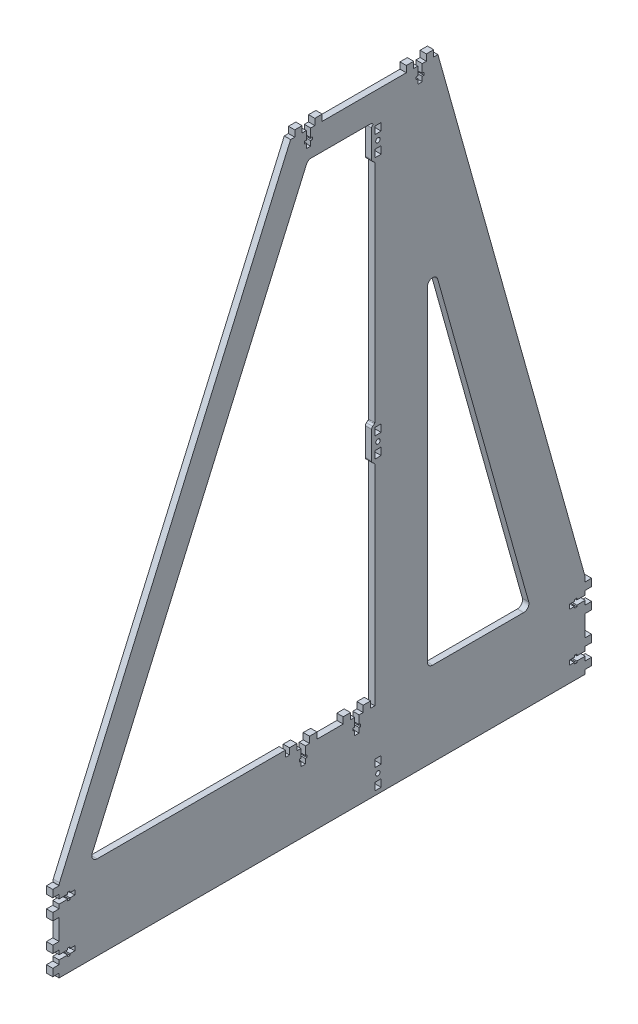
SolidWorks part; units mm, degrees
material "Клен"
ref_plane "Спереди" through (0, 0, 0) normal (0, 0, 1) x (1, 0, 0)
ref_plane "Сверху" through (0, 0, 0) normal (0, 1, 0) x (1, 0, 0)
ref_plane "Справа" through (0, 0, 0) normal (1, 0, 0) x (0, 0, -1)
sketch "боковина" plane through (0, 0, 0) normal (1, 0, 0) x (0, 0, -1)
  line L0 (-623.8891, -244.3792) -> (-123.8891, -244.3792)
  line L1 (-123.8891, -244.3792) -> (-123.8891, -165.066)
  line L2 (-124.0743, -163.7178) -> (-263.8891, 335.6208)
  line L3 (-263.8891, 335.6208) -> (-313.8032, 335.6208)
  line L4 (-323.8891, 305.6208) -> (-323.8891, -164.3792)
  line L5 (-408.8787, -164.3792) -> (-587.7577, -164.3792)
  line L6 (-623.8891, -168.1598) -> (-623.8891, -244.3792)
  line L7 (-268.8891, -164.3792) -> (-182.4044, -164.3792)
  line L8 (-177.5896, -158.031) -> (-264.0743, 150.8428)
  line L9 (-273.8891, 149.4947) -> (-273.8891, -159.3792)
  line L10 (-623.4697, -166.1553) -> (-403.8891, 335.6208)
  line L11 (-403.8891, 335.6208) -> (-313.8032, 335.6208)
  line L12 (-592.3383, -157.3747) -> (-388.8512, 307.6253)
  line L13 (-384.2706, 310.6208) -> (-328.8891, 310.6208)
  line L14 (-323.8891, -164.3792) -> (-323.8891, -170.3792)
  line L15 (-323.8891, -170.3792) -> (-408.8787, -170.3792)
  line L16 (-408.8787, -170.3792) -> (-408.8787, -164.3792)
  arc A0 (-264.0743, 150.8428) -> (-273.8891, 149.4947) centre (-268.8891, 149.4947) ccw
  arc A1 (-182.4044, -164.3792) -> (-177.5896, -158.031) centre (-182.4044, -159.3792) ccw
  arc A2 (-268.8891, -164.3792) -> (-273.8891, -159.3792) centre (-268.8891, -159.3792) cw
  arc A4 (-592.3383, -157.3747) -> (-587.7577, -164.3792) centre (-587.7577, -159.3792) ccw
  arc A5 (-328.8891, 310.6208) -> (-323.8891, 305.6208) centre (-328.8891, 305.6208) cw
  arc A6 (-384.2706, 310.6208) -> (-388.8512, 307.6253) centre (-384.2706, 305.6208) ccw
  arc A7 (-623.4697, -166.1553) -> (-623.8891, -168.1598) centre (-618.8891, -168.1598) ccw
  arc A8 (-123.8891, -165.066) -> (-124.0743, -163.7178) centre (-128.8891, -165.066) ccw
  point P25 (-323.8891, -164.3792)
  point P34 (-623.8891, -167.1137)
  point P37 (-123.8891, -164.3792)
  point P38 (-358.8462, 335.6208)
  dimension "D10" = 5
  dimension "D11" = 5
  dimension "D12" = 5
  dimension "D1" = 80
  dimension "D2" = 60
  dimension "D6" = 300
  dimension "D7" = 50
  dimension "D8" = 50
  dimension "D4" = 500
  dimension "D5" = 80
  dimension "D3" = 200
  dimension "D9" = 25
  dimension "D13" = 80
  dimension "D14" = 25
  dimension "D15" = 6
extrude "Бобышка-боковина" add sketch "боковина" along normal blind 6
ref_plane "Плоскость1" through (3, 0, 0) normal (1, 0, 0) x (0, 0, -1)
sketch "Эскиз2" plane through (6, 285.6208, 386.8891) normal (1, 0, 0) x (0, 0, -1)
  line L1 (-13.0318, 50) -> (-6.0318, 50)
  line L2 (-13.0318, 50) -> (-13.0318, 56)
  line L3 (-13.0318, 56) -> (-6.0318, 56)
  line L4 (-6.0318, 50) -> (-6.0318, 56)
  line L5 (13, 56) -> (-13, 56) construction
  line L7 (13.0318, 50) -> (6.0318, 50)
  line L8 (6.0318, 50) -> (6.0318, 56)
  line L9 (13.0318, 56) -> (6.0318, 56)
  line L10 (13.0318, 50) -> (13.0318, 56)
  dimension "D1" = 7
extrude "Бобышка-Вытянуть2" add sketch "Эскиз2" against normal blind 6
sketch "Эскиз3" plane through (6, 285.6208, 386.8891) normal (1, 0, 0) x (0, 0, -1)
  line L3 (-2.1, 42) -> (-3.6, 42)
  line L4 (-3.6, 42) -> (-3.6, 39.6)
  line L5 (-3.6, 39.6) -> (-2.1, 39.6)
  line L11 (3.6, 39.6) -> (2.1, 39.6)
  line L12 (3.6, 42) -> (3.6, 39.6)
  line L13 (2.1, 42) -> (3.6, 42)
  line L16 (-2.1, 42) -> (-2.1, 50)
  line L17 (-2.1, 50) -> (2.1, 50)
  line L18 (2.1, 50) -> (2.1, 42)
  line L19 (2.1, 39.6) -> (2.1, 35)
  line L20 (2.1, 35) -> (-2.1, 35)
  line L21 (-2.1, 35) -> (-2.1, 39.6)
  line L22 (13, 50) -> (-13, 50) construction
  point P15 (0, 43.65)
  point P20 (0, 50)
  dimension "D2" = 7.2
  dimension "D3" = 2.4
  dimension "D4" = 4.2
  dimension "D5" = 15
extrude "Вырез-Вытянуть1" cut sketch "Эскиз3" against normal through all
other "Авто-элемент1<DIN967-1>"
sketch "Эскиз21" plane through (6, 285.6208, 280.8891) normal (1, 0, 0) x (0, 0, -1)
  line L1 (-13.0318, 50) -> (-6.0318, 50)
  line L2 (-13.0318, 50) -> (-13.0318, 56)
  line L3 (-13.0318, 56) -> (-6.0318, 56)
  line L4 (-6.0318, 50) -> (-6.0318, 56)
  line L5 (13, 56) -> (-13, 56) construction
  line L7 (13.0318, 50) -> (6.0318, 50)
  line L8 (6.0318, 50) -> (6.0318, 56)
  line L9 (13.0318, 56) -> (6.0318, 56)
  line L10 (13.0318, 50) -> (13.0318, 56)
  dimension "D1" = 7
extrude "Бобышка-Вытянуть21" add sketch "Эскиз21" against normal blind 6
sketch "Эскиз31" plane through (6, 285.6208, 280.8891) normal (1, 0, 0) x (0, 0, -1)
  line L3 (-2.1, 42) -> (-3.6, 42)
  line L4 (-3.6, 42) -> (-3.6, 39.6)
  line L5 (-3.6, 39.6) -> (-2.1, 39.6)
  line L11 (3.6, 39.6) -> (2.1, 39.6)
  line L12 (3.6, 42) -> (3.6, 39.6)
  line L13 (2.1, 42) -> (3.6, 42)
  line L16 (-2.1, 42) -> (-2.1, 50)
  line L17 (-2.1, 50) -> (2.1, 50)
  line L18 (2.1, 50) -> (2.1, 42)
  line L19 (2.1, 39.6) -> (2.1, 35)
  line L20 (2.1, 35) -> (-2.1, 35)
  line L21 (-2.1, 35) -> (-2.1, 39.6)
  line L22 (13, 50) -> (-13, 50) construction
  point P15 (0, 43.65)
  point P20 (0, 50)
  dimension "D2" = 7.2
  dimension "D3" = 2.4
  dimension "D4" = 4.2
  dimension "D5" = 15
extrude "Вырез-Вытянуть11" cut sketch "Эскиз31" against normal through all
other "Авто-элемент2<DIN967-2>"
sketch "Эскиз22" plane through (0, 285.6208, 386.8891) normal (-1, 0, 0) x (0, 0, 1)
  line L1 (-13.0318, 50) -> (-6.0318, 50)
  line L2 (-13.0318, 50) -> (-13.0318, 56)
  line L3 (-13.0318, 56) -> (-6.0318, 56)
  line L4 (-6.0318, 50) -> (-6.0318, 56)
  line L5 (13, 56) -> (-13, 56) construction
  line L7 (13.0318, 50) -> (6.0318, 50)
  line L8 (6.0318, 50) -> (6.0318, 56)
  line L9 (13.0318, 56) -> (6.0318, 56)
  line L10 (13.0318, 50) -> (13.0318, 56)
  dimension "D1" = 7
extrude "Бобышка-Вытянуть22" add sketch "Эскиз22" against normal blind 6
other "Авто-элемент3<DIN967-3>"
sketch "Эскиз23" plane through (0, 285.6208, 280.8891) normal (-1, 0, 0) x (0, 0, 1)
  line L1 (-13.0318, 50) -> (-6.0318, 50)
  line L2 (-13.0318, 50) -> (-13.0318, 56)
  line L3 (-13.0318, 56) -> (-6.0318, 56)
  line L4 (-6.0318, 50) -> (-6.0318, 56)
  line L5 (13, 56) -> (-13, 56) construction
  line L7 (13.0318, 50) -> (6.0318, 50)
  line L8 (6.0318, 50) -> (6.0318, 56)
  line L9 (13.0318, 56) -> (6.0318, 56)
  line L10 (13.0318, 50) -> (13.0318, 56)
  dimension "D1" = 7
extrude "Бобышка-Вытянуть23" add sketch "Эскиз23" against normal blind 6
other "Авто-элемент4<DIN967-4>"
sketch "Эскиз24" plane through (0, -181.4615, 573.8891) normal (-1, 0, 0) x (0, -1, 0)
  line L1 (-13.0318, 50) -> (-6.0318, 50)
  line L2 (-13.0318, 50) -> (-13.0318, 56)
  line L3 (-13.0318, 56) -> (-6.0318, 56)
  line L4 (-6.0318, 50) -> (-6.0318, 56)
  line L5 (13, 56) -> (-13, 56) construction
  line L7 (13.0318, 50) -> (6.0318, 50)
  line L8 (6.0318, 50) -> (6.0318, 56)
  line L9 (13.0318, 56) -> (6.0318, 56)
  line L10 (13.0318, 50) -> (13.0318, 56)
  dimension "D1" = 7
extrude "Бобышка-Вытянуть24" add sketch "Эскиз24" against normal blind 6
sketch "Эскиз34" plane through (0, -181.4615, 573.8891) normal (-1, 0, 0) x (0, -1, 0)
  line L3 (-2.1, 42) -> (-3.6, 42)
  line L4 (-3.6, 42) -> (-3.6, 39.6)
  line L5 (-3.6, 39.6) -> (-2.1, 39.6)
  line L11 (3.6, 39.6) -> (2.1, 39.6)
  line L12 (3.6, 42) -> (3.6, 39.6)
  line L13 (2.1, 42) -> (3.6, 42)
  line L16 (-2.1, 42) -> (-2.1, 50)
  line L17 (-2.1, 50) -> (2.1, 50)
  line L18 (2.1, 50) -> (2.1, 42)
  line L19 (2.1, 39.6) -> (2.1, 35)
  line L20 (2.1, 35) -> (-2.1, 35)
  line L21 (-2.1, 35) -> (-2.1, 39.6)
  line L22 (13, 50) -> (-13, 50) construction
  point P15 (0, 43.65)
  point P20 (0, 50)
  dimension "D2" = 7.2
  dimension "D3" = 2.4
  dimension "D4" = 4.2
  dimension "D5" = 15
extrude "Вырез-Вытянуть14" cut sketch "Эскиз34" against normal through all
other "Авто-элемент5<DIN967-5>"
sketch "Эскиз25" plane through (0, -227.3792, 573.8891) normal (-1, 0, 0) x (0, -1, 0)
  line L1 (-13.0318, 50) -> (-6.0318, 50)
  line L2 (-13.0318, 50) -> (-13.0318, 56)
  line L3 (-13.0318, 56) -> (-6.0318, 56)
  line L4 (-6.0318, 50) -> (-6.0318, 56)
  line L5 (13, 56) -> (-13, 56) construction
  line L7 (13.0318, 50) -> (6.0318, 50)
  line L8 (6.0318, 50) -> (6.0318, 56)
  line L9 (13.0318, 56) -> (6.0318, 56)
  line L10 (13.0318, 50) -> (13.0318, 56)
  dimension "D1" = 7
extrude "Бобышка-Вытянуть25" add sketch "Эскиз25" against normal blind 6
sketch "Эскиз35" plane through (0, -227.3792, 573.8891) normal (-1, 0, 0) x (0, -1, 0)
  line L3 (-2.1, 42) -> (-3.6, 42)
  line L4 (-3.6, 42) -> (-3.6, 39.6)
  line L5 (-3.6, 39.6) -> (-2.1, 39.6)
  line L11 (3.6, 39.6) -> (2.1, 39.6)
  line L12 (3.6, 42) -> (3.6, 39.6)
  line L13 (2.1, 42) -> (3.6, 42)
  line L16 (-2.1, 42) -> (-2.1, 50)
  line L17 (-2.1, 50) -> (2.1, 50)
  line L18 (2.1, 50) -> (2.1, 42)
  line L19 (2.1, 39.6) -> (2.1, 35)
  line L20 (2.1, 35) -> (-2.1, 35)
  line L21 (-2.1, 35) -> (-2.1, 39.6)
  line L22 (13, 50) -> (-13, 50) construction
  point P15 (0, 43.65)
  point P20 (0, 50)
  dimension "D2" = 7.2
  dimension "D3" = 2.4
  dimension "D4" = 4.2
  dimension "D5" = 15
extrude "Вырез-Вытянуть15" cut sketch "Эскиз35" against normal through all
other "Авто-элемент6<DIN967-6>"
sketch "Эскиз26" plane through (6, -181.4615, 573.8891) normal (1, 0, 0) x (0, 1, 0)
  line L1 (-13.0318, 50) -> (-6.0318, 50)
  line L2 (-13.0318, 50) -> (-13.0318, 56)
  line L3 (-13.0318, 56) -> (-6.0318, 56)
  line L4 (-6.0318, 50) -> (-6.0318, 56)
  line L5 (13, 56) -> (-13, 56) construction
  line L7 (13.0318, 50) -> (6.0318, 50)
  line L8 (6.0318, 50) -> (6.0318, 56)
  line L9 (13.0318, 56) -> (6.0318, 56)
  line L10 (13.0318, 50) -> (13.0318, 56)
  dimension "D1" = 7
extrude "Бобышка-Вытянуть26" add sketch "Эскиз26" against normal blind 6
other "Авто-элемент7<DIN967-7>"
sketch "Эскиз27" plane through (6, -227.3792, 573.8891) normal (1, 0, 0) x (0, 1, 0)
  line L1 (-13.0318, 50) -> (-6.0318, 50)
  line L2 (-13.0318, 50) -> (-13.0318, 56)
  line L3 (-13.0318, 56) -> (-6.0318, 56)
  line L4 (-6.0318, 50) -> (-6.0318, 56)
  line L5 (13, 56) -> (-13, 56) construction
  line L7 (13.0318, 50) -> (6.0318, 50)
  line L8 (6.0318, 50) -> (6.0318, 56)
  line L9 (13.0318, 56) -> (6.0318, 56)
  line L10 (13.0318, 50) -> (13.0318, 56)
  dimension "D1" = 7
extrude "Бобышка-Вытянуть27" add sketch "Эскиз27" against normal blind 6
other "Авто-элемент8<DIN967-8>"
sketch "Эскиз28" plane through (6, -181.3792, 173.8891) normal (1, 0, 0) x (0, -1, 0)
  line L1 (-13.0318, 50) -> (-6.0318, 50)
  line L2 (-13.0318, 50) -> (-13.0318, 56)
  line L3 (-13.0318, 56) -> (-6.0318, 56)
  line L4 (-6.0318, 50) -> (-6.0318, 56)
  line L5 (13, 56) -> (-13, 56) construction
  line L7 (13.0318, 50) -> (6.0318, 50)
  line L8 (6.0318, 50) -> (6.0318, 56)
  line L9 (13.0318, 56) -> (6.0318, 56)
  line L10 (13.0318, 50) -> (13.0318, 56)
  dimension "D1" = 7
extrude "Бобышка-Вытянуть28" add sketch "Эскиз28" against normal blind 6
sketch "Эскиз38" plane through (6, -181.3792, 173.8891) normal (1, 0, 0) x (0, -1, 0)
  line L3 (-2.1, 42) -> (-3.6, 42)
  line L4 (-3.6, 42) -> (-3.6, 39.6)
  line L5 (-3.6, 39.6) -> (-2.1, 39.6)
  line L11 (3.6, 39.6) -> (2.1, 39.6)
  line L12 (3.6, 42) -> (3.6, 39.6)
  line L13 (2.1, 42) -> (3.6, 42)
  line L16 (-2.1, 42) -> (-2.1, 50)
  line L17 (-2.1, 50) -> (2.1, 50)
  line L18 (2.1, 50) -> (2.1, 42)
  line L19 (2.1, 39.6) -> (2.1, 35)
  line L20 (2.1, 35) -> (-2.1, 35)
  line L21 (-2.1, 35) -> (-2.1, 39.6)
  line L22 (13, 50) -> (-13, 50) construction
  point P15 (0, 43.65)
  point P20 (0, 50)
  dimension "D2" = 7.2
  dimension "D3" = 2.4
  dimension "D4" = 4.2
  dimension "D5" = 15
extrude "Вырез-Вытянуть18" cut sketch "Эскиз38" against normal through all
other "Авто-элемент9<DIN967-9>"
sketch "Эскиз29" plane through (6, -227.3792, 173.8891) normal (1, 0, 0) x (0, -1, 0)
  line L1 (-13.0318, 50) -> (-6.0318, 50)
  line L2 (-13.0318, 50) -> (-13.0318, 56)
  line L3 (-13.0318, 56) -> (-6.0318, 56)
  line L4 (-6.0318, 50) -> (-6.0318, 56)
  line L5 (13, 56) -> (-13, 56) construction
  line L7 (13.0318, 50) -> (6.0318, 50)
  line L8 (6.0318, 50) -> (6.0318, 56)
  line L9 (13.0318, 56) -> (6.0318, 56)
  line L10 (13.0318, 50) -> (13.0318, 56)
  dimension "D1" = 7
extrude "Бобышка-Вытянуть29" add sketch "Эскиз29" against normal blind 6
sketch "Эскиз39" plane through (6, -227.3792, 173.8891) normal (1, 0, 0) x (0, -1, 0)
  line L3 (-2.1, 42) -> (-3.6, 42)
  line L4 (-3.6, 42) -> (-3.6, 39.6)
  line L5 (-3.6, 39.6) -> (-2.1, 39.6)
  line L11 (3.6, 39.6) -> (2.1, 39.6)
  line L12 (3.6, 42) -> (3.6, 39.6)
  line L13 (2.1, 42) -> (3.6, 42)
  line L16 (-2.1, 42) -> (-2.1, 50)
  line L17 (-2.1, 50) -> (2.1, 50)
  line L18 (2.1, 50) -> (2.1, 42)
  line L19 (2.1, 39.6) -> (2.1, 35)
  line L20 (2.1, 35) -> (-2.1, 35)
  line L21 (-2.1, 35) -> (-2.1, 39.6)
  line L22 (13, 50) -> (-13, 50) construction
  point P15 (0, 43.65)
  point P20 (0, 50)
  dimension "D2" = 7.2
  dimension "D3" = 2.4
  dimension "D4" = 4.2
  dimension "D5" = 15
extrude "Вырез-Вытянуть19" cut sketch "Эскиз39" against normal through all
other "Авто-элемент10<DIN967-10>"
sketch "Эскиз210" plane through (0, -181.3792, 173.8891) normal (-1, 0, 0) x (0, 1, 0)
  line L1 (-13.0318, 50) -> (-6.0318, 50)
  line L2 (-13.0318, 50) -> (-13.0318, 56)
  line L3 (-13.0318, 56) -> (-6.0318, 56)
  line L4 (-6.0318, 50) -> (-6.0318, 56)
  line L5 (13, 56) -> (-13, 56) construction
  line L7 (13.0318, 50) -> (6.0318, 50)
  line L8 (6.0318, 50) -> (6.0318, 56)
  line L9 (13.0318, 56) -> (6.0318, 56)
  line L10 (13.0318, 50) -> (13.0318, 56)
  dimension "D1" = 7
extrude "Бобышка-Вытянуть210" add sketch "Эскиз210" against normal blind 6
other "Авто-элемент11<DIN967-12>"
sketch "Эскиз211" plane through (0, -227.3792, 173.8891) normal (-1, 0, 0) x (0, 1, 0)
  line L1 (-13.0318, 50) -> (-6.0318, 50)
  line L2 (-13.0318, 50) -> (-13.0318, 56)
  line L3 (-13.0318, 56) -> (-6.0318, 56)
  line L4 (-6.0318, 50) -> (-6.0318, 56)
  line L5 (13, 56) -> (-13, 56) construction
  line L7 (13.0318, 50) -> (6.0318, 50)
  line L8 (6.0318, 50) -> (6.0318, 56)
  line L9 (13.0318, 56) -> (6.0318, 56)
  line L10 (13.0318, 50) -> (13.0318, 56)
  dimension "D1" = 7
extrude "Бобышка-Вытянуть211" add sketch "Эскиз211" against normal blind 6
other "Авто-элемент12<DIN967-11>"
sketch "Эскиз312" plane through (6, -227.3792, 273.8891) normal (1, 0, 0) x (0, 1, 0)
  line L1 (13.0318, 50) -> (6.0318, 50)
  line L2 (13.0318, 50) -> (13.0318, 44)
  line L3 (13.0318, 44) -> (6.0318, 44)
  line L4 (6.0318, 50) -> (6.0318, 44)
  line L5 (-13.0318, 44) -> (-6.0318, 44)
  line L6 (-13.0318, 50) -> (-13.0318, 44)
  line L7 (-6.0318, 50) -> (-6.0318, 44)
  line L8 (-13.0318, 50) -> (-6.0318, 50)
  circle A0 centre (0, 47) radius 2.1
  dimension "D1" = 4.2
extrude "Вырез-Вытянуть112" cut sketch "Эскиз312" against normal through all
other "Авто-элемент13<DIN967-14>"
sketch "Эскиз212" plane through (0, 45.6208, 273.8891) normal (1, 0, 0) x (0, 1, 0)
  line L0 (-13, 53) -> (13, 53)
  line L2 (15, 52) -> (16.2, 50.4)
  line L4 (17, 50) -> (-17, 50)
  line L5 (-15, 52) -> (-16.2, 50.4)
  arc A6 (13, 53) -> (15, 52) centre (13, 50.5) cw
  arc A7 (16.2, 50.4) -> (17, 50) centre (17, 51) ccw
  arc A8 (-13, 53) -> (-15, 52) centre (-13, 50.5) ccw
  arc A9 (-16.2, 50.4) -> (-17, 50) centre (-17, 51) cw
  point P12 (0, 53)
  point P13 (14.118, 52.7361)
  point P15 (-14.118, 52.7361)
  point P17 (0, 50)
  point P21 (14.118, 52.7361)
  dimension "D4" = 2.5
  dimension "D5" = 1
extrude "Бобышка-Вытянуть212" add sketch "Эскиз212" along normal blind 6
sketch "Эскиз313" plane through (6, 45.6208, 273.8891) normal (1, 0, 0) x (0, 1, 0)
  line L1 (13.0318, 50) -> (6.0318, 50)
  line L2 (13.0318, 50) -> (13.0318, 44)
  line L3 (13.0318, 44) -> (6.0318, 44)
  line L4 (6.0318, 50) -> (6.0318, 44)
  line L5 (-13.0318, 44) -> (-6.0318, 44)
  line L6 (-13.0318, 50) -> (-13.0318, 44)
  line L7 (-6.0318, 50) -> (-6.0318, 44)
  line L8 (-13.0318, 50) -> (-6.0318, 50)
  circle A0 centre (0, 47) radius 2.1
  dimension "D1" = 4.2
extrude "Вырез-Вытянуть113" cut sketch "Эскиз313" against normal through all
other "Авто-элемент14<DIN967-15>"
sketch "Эскиз213" plane through (6, 45.6208, 273.8891) normal (-1, 0, 0) x (0, -1, 0)
  line L0 (-13, 53) -> (13, 53)
  line L2 (15, 52) -> (16.2, 50.4)
  line L4 (17, 50) -> (-17, 50)
  line L5 (-15, 52) -> (-16.2, 50.4)
  arc A6 (13, 53) -> (15, 52) centre (13, 50.5) cw
  arc A7 (16.2, 50.4) -> (17, 50) centre (17, 51) ccw
  arc A8 (-13, 53) -> (-15, 52) centre (-13, 50.5) ccw
  arc A9 (-16.2, 50.4) -> (-17, 50) centre (-17, 51) cw
  point P12 (0, 53)
  point P13 (14.118, 52.7361)
  point P15 (-14.118, 52.7361)
  point P17 (0, 50)
  point P21 (14.118, 52.7361)
  dimension "D4" = 2.5
  dimension "D5" = 1
extrude "Бобышка-Вытянуть213" add sketch "Эскиз213" along normal blind 6
other "Авто-элемент15<DIN967-16>"
sketch "Эскиз214" plane through (6, 293.6208, 273.8891) normal (-1, 0, 0) x (0, -1, 0)
  line L0 (-13, 53) -> (13, 53)
  line L2 (15, 52) -> (16.2, 50.4)
  line L4 (17, 50) -> (-17, 50)
  line L5 (-15, 52) -> (-16.2, 50.4)
  arc A6 (13, 53) -> (15, 52) centre (13, 50.5) cw
  arc A7 (16.2, 50.4) -> (17, 50) centre (17, 51) ccw
  arc A8 (-13, 53) -> (-15, 52) centre (-13, 50.5) ccw
  arc A9 (-16.2, 50.4) -> (-17, 50) centre (-17, 51) cw
  point P12 (0, 53)
  point P13 (14.118, 52.7361)
  point P15 (-14.118, 52.7361)
  point P17 (0, 50)
  point P21 (14.118, 52.7361)
  dimension "D4" = 2.5
  dimension "D5" = 1
extrude "Бобышка-Вытянуть214" add sketch "Эскиз214" along normal blind 6
sketch "Эскиз315" plane through (0, 293.6208, 273.8891) normal (-1, 0, 0) x (0, -1, 0)
  line L1 (13.0318, 50) -> (6.0318, 50)
  line L2 (13.0318, 50) -> (13.0318, 44)
  line L3 (13.0318, 44) -> (6.0318, 44)
  line L4 (6.0318, 50) -> (6.0318, 44)
  line L5 (-13.0318, 44) -> (-6.0318, 44)
  line L6 (-13.0318, 50) -> (-13.0318, 44)
  line L7 (-6.0318, 50) -> (-6.0318, 44)
  line L8 (-13.0318, 50) -> (-6.0318, 50)
  circle A0 centre (0, 47) radius 2.1
  dimension "D1" = 4.2
extrude "Вырез-Вытянуть115" cut sketch "Эскиз315" against normal through all
other "Авто-элемент16<DIN967-17>"
sketch "Эскиз215" plane through (0, 293.6208, 273.8891) normal (1, 0, 0) x (0, 1, 0)
  line L0 (-13, 53) -> (13, 53)
  line L2 (15, 52) -> (16.2, 50.4)
  line L4 (17, 50) -> (-17, 50)
  line L5 (-15, 52) -> (-16.2, 50.4)
  arc A6 (13, 53) -> (15, 52) centre (13, 50.5) cw
  arc A7 (16.2, 50.4) -> (17, 50) centre (17, 51) ccw
  arc A8 (-13, 53) -> (-15, 52) centre (-13, 50.5) ccw
  arc A9 (-16.2, 50.4) -> (-17, 50) centre (-17, 51) cw
  point P12 (0, 53)
  point P13 (14.118, 52.7361)
  point P15 (-14.118, 52.7361)
  point P17 (0, 50)
  point P21 (14.118, 52.7361)
  dimension "D4" = 2.5
  dimension "D5" = 1
extrude "Бобышка-Вытянуть215" add sketch "Эскиз215" along normal blind 6
other "Авто-элемент18<DIN967-19>"
sketch "Эскиз216" plane through (6, -220.3792, 340.8891) normal (1, 0, 0) x (0, 0, -1)
  line L1 (-13.0318, 50) -> (-6.0318, 50)
  line L2 (-13.0318, 50) -> (-13.0318, 56)
  line L3 (-13.0318, 56) -> (-6.0318, 56)
  line L4 (-6.0318, 50) -> (-6.0318, 56)
  line L5 (13, 56) -> (-13, 56) construction
  line L7 (13.0318, 50) -> (6.0318, 50)
  line L8 (6.0318, 50) -> (6.0318, 56)
  line L9 (13.0318, 56) -> (6.0318, 56)
  line L10 (13.0318, 50) -> (13.0318, 56)
  dimension "D1" = 7
extrude "Бобышка-Вытянуть216" add sketch "Эскиз216" against normal blind 6
sketch "Эскиз318" plane through (6, -220.3792, 340.8891) normal (1, 0, 0) x (0, 0, -1)
  line L3 (-2.1, 42) -> (-3.6, 42)
  line L4 (-3.6, 42) -> (-3.6, 39.6)
  line L5 (-3.6, 39.6) -> (-2.1, 39.6)
  line L11 (3.6, 39.6) -> (2.1, 39.6)
  line L12 (3.6, 42) -> (3.6, 39.6)
  line L13 (2.1, 42) -> (3.6, 42)
  line L16 (-2.1, 42) -> (-2.1, 50)
  line L17 (-2.1, 50) -> (2.1, 50)
  line L18 (2.1, 50) -> (2.1, 42)
  line L19 (2.1, 39.6) -> (2.1, 35)
  line L20 (2.1, 35) -> (-2.1, 35)
  line L21 (-2.1, 35) -> (-2.1, 39.6)
  line L22 (13, 50) -> (-13, 50) construction
  point P15 (0, 43.65)
  point P20 (0, 50)
  dimension "D2" = 7.2
  dimension "D3" = 2.4
  dimension "D4" = 4.2
  dimension "D5" = 15
extrude "Вырез-Вытянуть118" cut sketch "Эскиз318" against normal through all
other "Авто-элемент19<DIN967-22>"
sketch "Эскиз218" plane through (6, -220.3792, 391.8891) normal (1, 0, 0) x (0, 0, -1)
  line L1 (-13.0318, 50) -> (-6.0318, 50)
  line L2 (-13.0318, 50) -> (-13.0318, 56)
  line L3 (-13.0318, 56) -> (-6.0318, 56)
  line L4 (-6.0318, 50) -> (-6.0318, 56)
  line L5 (13, 56) -> (-13, 56) construction
  line L6 (0, 53.4074) -> (0, -162.0434) construction
  line L7 (13.0318, 50) -> (6.0318, 50)
  line L8 (6.0318, 50) -> (6.0318, 56)
  line L9 (13.0318, 56) -> (6.0318, 56)
  line L10 (13.0318, 50) -> (13.0318, 56)
  dimension "D1" = 7
extrude "Бобышка-Вытянуть219" add sketch "Эскиз218" against normal blind 6
sketch "Эскиз321" plane through (6, -220.3792, 391.8891) normal (1, 0, 0) x (0, 0, -1)
  line L3 (-2.1, 42) -> (-3.6, 42)
  line L4 (-3.6, 42) -> (-3.6, 39.6)
  line L5 (-3.6, 39.6) -> (-2.1, 39.6)
  line L8 (0, 53.4074) -> (0, -162.0434) construction
  line L11 (3.6, 39.6) -> (2.1, 39.6)
  line L12 (3.6, 42) -> (3.6, 39.6)
  line L13 (2.1, 42) -> (3.6, 42)
  line L16 (-2.1, 42) -> (-2.1, 50)
  line L17 (-2.1, 50) -> (2.1, 50)
  line L18 (2.1, 50) -> (2.1, 42)
  line L19 (2.1, 39.6) -> (2.1, 35)
  line L20 (2.1, 35) -> (-2.1, 35)
  line L21 (-2.1, 35) -> (-2.1, 39.6)
  point P15 (0, 43.65)
  point P20 (0, 50)
  dimension "D2" = 7.2
  dimension "D3" = 2.4
  dimension "D4" = 4.2
extrude "Вырез-Вытянуть121" cut sketch "Эскиз321" against normal through all
other "Авто-элемент2<DIN967_2-2>"
equation "\"D7@боковина\"=\"D8@боковина\""
equation "\"sheet_thickness\"= 6"
equation "\"bottom_line\"= 60"
equation "\"width_space\"= 500"
equation "\"D5@боковина\"=\"D1@боковина\""
